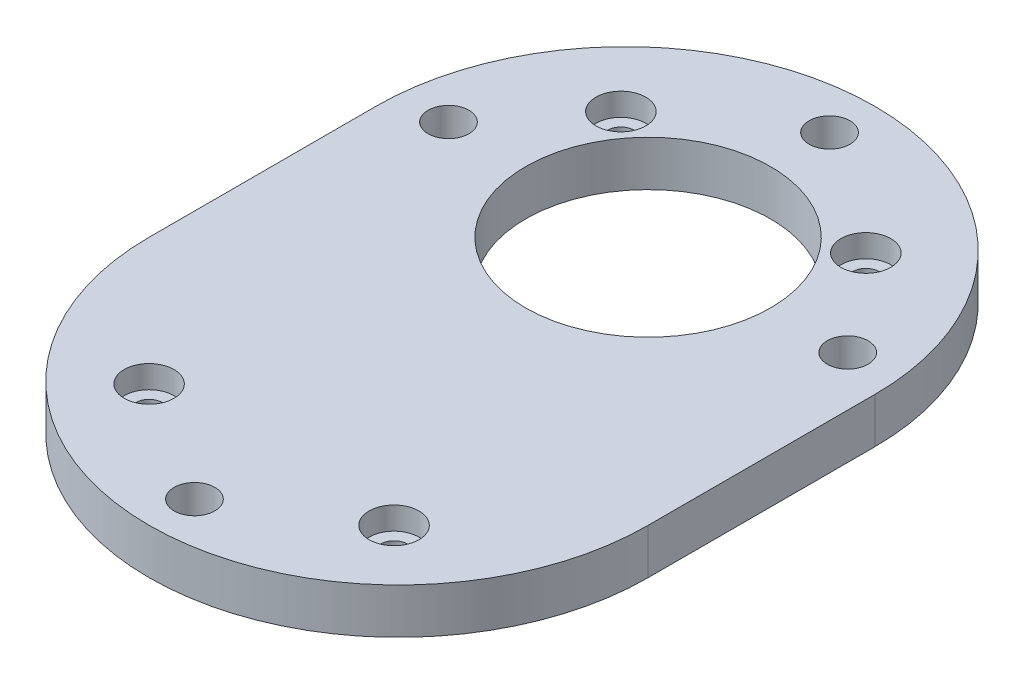
SolidWorks part; units mm, degrees
ref_plane "정면" through (0, 0, 0) normal (0, 0, 1) x (1, 0, 0)
ref_plane "윗면" through (0, 0, 0) normal (0, 1, 0) x (1, 0, 0)
ref_plane "우측면" through (0, 0, 0) normal (1, 0, 0) x (0, 0, -1)
sketch "스케치1" plane through (0, 0, 0) normal (0, 1, 0) x (1, 0, 0)
  line L2 (-27.5, 15) -> (-27.5, -10)
  line L4 (27.5, 15) -> (27.5, -10)
  arc A1 (27.5, 15) -> (-27.5, 15) centre (0, 15) ccw
  arc A3 (-27.5, -10) -> (27.5, -10) centre (0, -10) ccw
  point P0 (0, 0)
  dimension "D4" = 55
  dimension "D1" = 27.5
  dimension "D2" = 55
  dimension "D5" = 27.5
extrude "보스-돌출1" add sketch "스케치1" along normal blind 5
sketch "스케치2" plane through (0, 5, 0) normal (0, 1, 0) x (1, 0, 0)
  line L0 (0, 0) -> (0, 50000) construction
  line L2 (-16.75, 42.5) -> (16.75, 42.5) construction
  line L3 (-16.75, 42.5) -> (-16.75, -37.5) construction
  line L4 (-16.75, -37.5) -> (16.75, -37.5) construction
  line L5 (16.75, 42.5) -> (16.75, -37.5) construction
  circle A0 centre (0, 17.5) radius 13.5
  circle A1 centre (-13.5, 28) radius 1.3 construction
  circle A2 centre (13.5, 28) radius 1.3 construction
  circle A3 centre (-13.5, -24) radius 1.3 construction
  circle A5 centre (13.5, -24) radius 1.3 construction
  arc A6 (27.5, 15) -> (-27.5, 15) centre (0, 15) ccw construction
  arc A8 (-27.5, -10) -> (27.5, -10) centre (0, -10) ccw construction
  dimension "D1" = 27
  dimension "D2" = 2.6
  dimension "D5" = 2.6
  dimension "D6" = 13.5
  dimension "D3" = 10.5
  dimension "D4" = 13.5
  dimension "D7" = 52
  dimension "D8" = 33.5
  dimension "D9" = 16.75
  dimension "D10" = 25
extrude "컷-돌출1" cut sketch "스케치2" against normal blind 5
sketch "스케치3" plane through (0, 5, 0) normal (0, 1, 0) x (1, 0, 0)
  line L1 (-16.75, 31.25) -> (16.75, 31.25) construction
  line L2 (-16.75, 31.25) -> (-16.75, -27.25) construction
  line L3 (-16.75, -27.25) -> (16.75, -27.25) construction
  line L4 (16.75, 31.25) -> (16.75, -27.25) construction
  line L5 (-27.5, 15) -> (-27.5, -10) construction
  circle A0 centre (0, 17.5) radius 25 construction
  dimension "D1" = 50
  dimension "D2" = 33.5
  dimension "D3" = 58.5
  dimension "D4" = 13.75
  dimension "D5" = 10.75
sketch "스케치4" plane through (0, 5, 0) normal (0, 1, 0) x (1, 0, 0)
  line L0 (0, 15) -> (0, 50015) construction
  line L1 (0, 17.5) -> (50000, 17.5) construction
  circle A0 centre (0, 37.5) radius 2.25
  circle A1 centre (0, 37.5) radius 4.5 construction
  circle A3 centre (0, -32.5) radius 2.25
  circle A4 centre (0, -32.5) radius 4.5 construction
  circle A5 centre (-22, 17.5) radius 2.25
  circle A6 centre (-22, 17.5) radius 4.5 construction
  circle A7 centre (22, 17.5) radius 2.25
  dimension "D1" = 4.5
  dimension "D3" = 9
  dimension "D4" = 4.5
  dimension "D6" = 9
  dimension "D7" = 4.5
  dimension "D9" = 9
  dimension "D10" = 4.5
  dimension "D2" = 20
  dimension "D5" = 50
  dimension "D8" = 22
  dimension "D11" = 22
extrude "컷-돌출2" cut sketch "스케치4" against normal blind 5
hole_wizard "M2.5 소켓 머리 캡 나사용 카운터보어1" positions "스케치6" profile "스케치7" counterbore size "M2.5" standard "KS" end condition through all
sketch "스케치6" plane through (0, 5, 0) normal (0, 1, 0) x (1, 0, 0)
  point P0 (-13.5, 28)
  point P3 (13.5, 28)
  point P6 (13.5, -24)
  point P9 (-13.5, -24)
sketch "스케치7" plane through (-13.5, 5, -28) normal (1, 0, 0) x (0, 0, 1)
  line L0 (0, 0) -> (0, 5)
  line L1 (0, 5) -> (1.45, 5)
  line L3 (1.45, 5) -> (1.45, 2.5)
  line L4 (1.45, 2.5) -> (2.75, 2.5)
  line L5 (2.75, 2.5) -> (2.75, 0)
  line L7 (2.75, 0) -> (0, 0)
  line L11 (0, -6.35) -> (0, 107.95) construction
  dimension "관통 구멍 지름" = 2.9
  dimension "관통 구멍 깊이" = 5
  dimension "카운터보어 지름" = 5.5
  dimension "카운터보어 깊이" = 2.5
